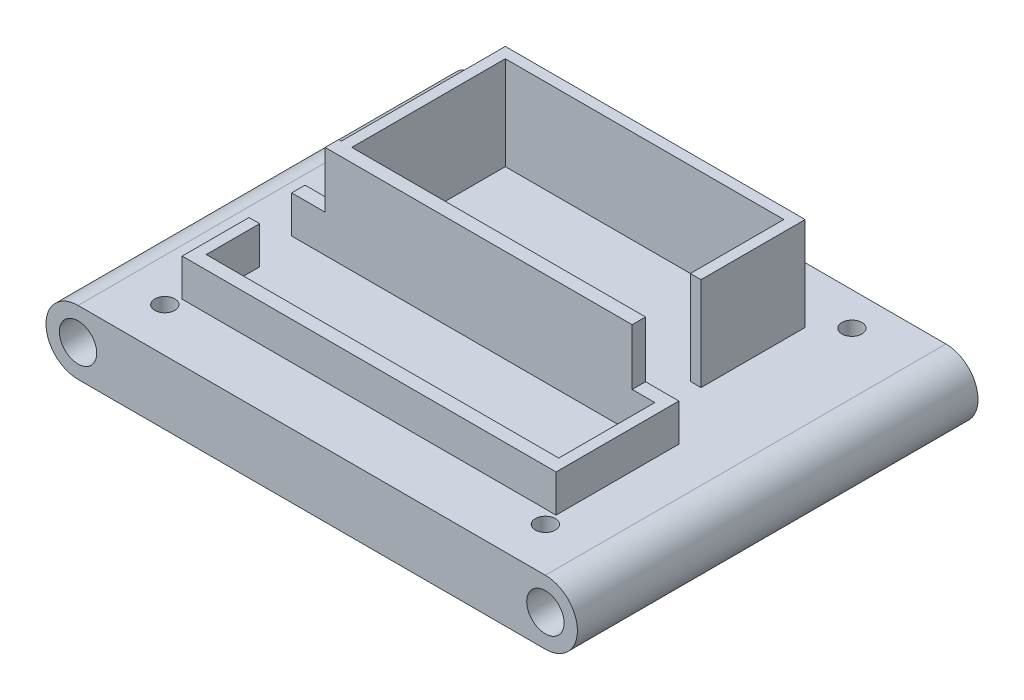
SolidWorks part; units mm, degrees
ref_plane "Front Plane" through (0, 0, 0) normal (0, 0, 1) x (1, 0, 0)
ref_plane "Top Plane" through (0, 0, 0) normal (0, 1, 0) x (1, 0, 0)
ref_plane "Right Plane" through (0, 0, 0) normal (1, 0, 0) x (0, 0, -1)
sketch "Sketch1" plane through (0, 0, 0) normal (0, 0, 1) x (1, 0, 0)
  line L0 (0, -55) -> (0, 55) construction
  line L1 (-44.45, 6.096) -> (44.45, 6.096)
  line L2 (-44.45, -6.096) -> (44.45, -6.096)
  arc A0 (44.45, -6.096) -> (44.45, 6.096) centre (44.45, 0) ccw
  arc A1 (-44.45, -6.096) -> (-44.45, 6.096) centre (-44.45, 0) cw
  circle A2 centre (-44.45, 0) radius 3.556
  circle A3 centre (44.45, 0) radius 3.556
extrude "Boss-Extrude1" add sketch "Sketch1" along normal blind 76.2
sketch "Sketch2" plane through (0, -6.096, 0) normal (0, -1, 0) x (1, 0, 0)
  circle A0 centre (-9.144, 69.215) radius 1.905
  circle A1 centre (27.051, 60.833) radius 1.905
  circle A2 centre (-28.956, 69.215) radius 1.905
  circle A3 centre (-28.956, 6.985) radius 1.905
  circle A4 centre (-9.144, 6.985) radius 1.905
  circle A5 centre (11.049, 60.833) radius 1.905
  circle A6 centre (11.049, 15.367) radius 1.905
  circle A7 centre (27.051, 15.367) radius 1.905
  dimension "D1" = 2
  dimension "D2" = 2
  dimension "D3" = 2
  dimension "D4" = 2
extrude "Cut-Extrude1" cut sketch "Sketch2" against normal blind 6.604
sketch "Sketch3" plane through (0, 6.096, 0) normal (0, 1, 0) x (1, 0, 0)
  line L1 (-29.21, -12.7) -> (28.8477, -12.7)
  line L2 (-29.21, -12.7) -> (-29.21, -10.16)
  line L3 (-29.21, -10.16) -> (28.8477, -10.16)
  line L4 (28.8477, -12.7) -> (28.8477, -10.16)
  line L5 (-29.21, -44.45) -> (29.21, -44.45)
  line L6 (-29.21, -44.45) -> (-29.21, -41.91)
  line L7 (-29.21, -41.91) -> (29.21, -41.91)
  line L8 (29.21, -44.45) -> (29.21, -41.91)
  line L9 (-29.21, -41.91) -> (-26.67, -41.91)
  line L10 (-29.21, -41.91) -> (-29.21, -15.24)
  line L11 (-29.21, -15.24) -> (-26.67, -15.24)
  line L12 (-26.67, -41.91) -> (-26.67, -15.24)
  line L17 (28.8477, -15.24) -> (26.3077, -15.24)
  line L18 (28.8477, -15.24) -> (28.8477, -30.48)
  line L19 (28.8477, -30.48) -> (26.3077, -30.48)
  line L20 (26.3077, -15.24) -> (26.3077, -30.48)
  line L21 (-29.21, -12.7) -> (-26.67, -12.7)
  line L22 (-29.21, -12.7) -> (-29.21, -15.24)
  line L23 (-29.21, -15.24) -> (-26.67, -15.24)
  line L24 (-26.67, -12.7) -> (-26.67, -15.24)
  line L25 (28.8477, -12.7) -> (26.3077, -12.7)
  line L26 (28.8477, -12.7) -> (28.8477, -15.24)
  line L27 (28.8477, -15.24) -> (26.3077, -15.24)
  line L28 (26.3077, -12.7) -> (26.3077, -15.24)
  point P0 (0, 0)
  point P1 (0, 0)
  dimension "D1" = 2.54
  dimension "D2" = 2.54
  dimension "D3" = 58.42
  dimension "D4" = 2.54
  dimension "D5" = 2.54
  dimension "D6" = 15.24
extrude "Boss-Extrude2" add sketch "Sketch3" along normal blind 17.78 contours L1 L4 L3 L2 | L7 L12 L1 L10 | L5 L8 L7 L6 | L24 L1 L22 L11 | L1 L28 L17 L26
sketch "Sketch4" plane through (0, 6.096, 0) normal (0, 1, 0) x (1, 0, 0)
  line L1 (29.21, -44.45) -> (36.068, -44.45)
  line L2 (29.21, -44.45) -> (29.21, -41.91)
  line L3 (29.21, -41.91) -> (36.068, -41.91)
  line L4 (36.068, -44.45) -> (36.068, -41.91)
  line L5 (-29.21, -44.45) -> (-36.068, -44.45)
  line L6 (-29.21, -44.45) -> (-29.21, -41.91)
  line L7 (-29.21, -41.91) -> (-36.068, -41.91)
  line L8 (-36.068, -44.45) -> (-36.068, -41.91)
  line L13 (36.068, -44.45) -> (33.528, -44.45)
  line L14 (36.068, -44.45) -> (36.068, -62.738)
  line L15 (36.068, -62.738) -> (33.528, -62.738)
  line L16 (33.528, -44.45) -> (33.528, -62.738)
  line L17 (-36.068, -62.738) -> (36.068, -62.738)
  line L18 (-36.068, -62.738) -> (-36.068, -65.278)
  line L19 (-36.068, -65.278) -> (36.068, -65.278)
  line L20 (36.068, -62.738) -> (36.068, -65.278)
  line L21 (-36.068, -62.738) -> (-33.528, -62.738)
  line L22 (-36.068, -62.738) -> (-36.068, -52.578)
  line L23 (-36.068, -52.578) -> (-33.528, -52.578)
  line L24 (-33.528, -62.738) -> (-33.528, -52.578)
  line M19 (-29.21, -44.45) -> (-29.21, -10.16)
  line M27 (29.21, -41.91) -> (29.21, -44.45)
  dimension "D1" = 6.858
  dimension "D2" = 6.858
  dimension "D3" = 10.16
  dimension "D5" = 18.288
  dimension "D6" = 2.54
  dimension "D7" = 2.54
extrude "Boss-Extrude3" add sketch "Sketch4" along normal blind 7.112 contours L8 L5 L7 M19 | L17 L24 L23 L22 | L20 L15 L17 L18 L19 | L1 L16 L15 L14 | L1 L4 L3 M27
sketch "Sketch5" plane through (0, 6.096, 0) normal (0, 1, 0) x (1, 0, 0)
  circle A2 centre (36.068, -67.818) radius 1.905
  circle A3 centre (32.9117, -6.35) radius 1.905
extrude "Cut-Extrude3" cut sketch "Sketch5" against normal blind 7.112 contours A2 | A3
sketch "Sketch6" plane through (0, 6.096, 0) normal (0, 1, 0) x (1, 0, 0)
  circle A0 centre (-36.322, -67.818) radius 1.905
  circle A1 centre (-33.274, -6.35) radius 1.905
extrude "Cut-Extrude4" cut sketch "Sketch6" against normal blind 7.112 contours A1 | A0
sketch "Sketch8" plane through (0, 23.876, 0) normal (0, 1, 0) x (1, 0, 0)
  line L2 (28.3397, -30.48) -> (28.3397, -10.16)
  line L3 (28.3397, -30.48) -> (28.3397, -10.16)
  line L4 (28.3397, -10.16) -> (28.8477, -10.16)
  line L5 (-28.702, -41.91) -> (-28.702, -10.16)
  line L6 (-28.702, -41.91) -> (-28.702, -10.16)
  line L7 (28.8477, -10.16) -> (28.8477, -30.48)
  line L8 (28.8477, -30.48) -> (28.3397, -30.48)
  line L9 (-28.702, -10.16) -> (-29.21, -10.16)
  line L10 (-29.21, -10.16) -> (-29.21, -41.8259)
  line L11 (-29.21, -44.45) -> (-29.21, -10.16) construction
  line L12 (-29.21, -41.8259) -> (-28.702, -41.91)
  dimension "D1" = 0.508
  dimension "D2" = 0.508
extrude "Cut-Extrude5" cut sketch "Sketch8" against normal up to surface (17.78 mm away) up to face at (-33.274, 6.096, 8.255)
sketch "Sketch9" plane through (0, 13.208, 0) normal (0, 1, 0) x (1, 0, 0)
  line L1 (-35.56, -41.91) -> (-36.068, -41.91)
  line L2 (-35.56, -44.45) -> (-35.56, -41.91)
  line L3 (-35.56, -44.45) -> (-35.56, -41.91)
  line L4 (-36.068, -41.91) -> (-36.068, -44.45)
  line L5 (-36.068, -44.45) -> (-35.56, -44.45)
  dimension "D1" = 0.508
extrude "Cut-Extrude6" cut sketch "Sketch9" against normal up to surface (7.112 mm away) up to face at (-6.6003, 6.096, 40.4072)
sketch "Sketch10" plane through (0, 13.208, 0) normal (0, 1, 0) x (1, 0, 0)
  line L8 (-35.56, -65.278) -> (-35.56, -52.578)
  line L9 (-35.56, -65.278) -> (-35.56, -52.578)
  line L10 (-35.56, -52.578) -> (-36.068, -52.578)
  line L11 (35.56, -41.91) -> (35.56, -65.278)
  line L12 (35.56, -41.91) -> (35.56, -65.278)
  line L13 (-36.068, -52.578) -> (-36.068, -65.278)
  line L14 (-36.068, -65.278) -> (-35.56, -65.278)
  line L15 (35.56, -41.91) -> (36.068, -41.91)
  line L16 (36.068, -41.91) -> (36.068, -65.278)
  line L17 (36.068, -65.278) -> (35.56, -65.278)
  line M3 (-36.068, -52.578) -> (-36.068, -65.278)
  line M4 (-36.068, -65.278) -> (36.068, -65.278)
  line M5 (36.068, -65.278) -> (36.068, -41.91)
  line M6 (36.068, -41.91) -> (29.21, -41.91)
  line M12 (-33.528, -52.578) -> (-36.068, -52.578)
  dimension "D1" = 0.508
  dimension "D2" = 0.508
extrude "Cut-Extrude7" cut sketch "Sketch10" against normal up to surface (7.112 mm away) contours L9 M4 M12 M3 | L12 M6 M4 M5 up to face at (-6.5495, 6.096, 40.4072)
sketch "Sketch11" plane through (0, 23.876, 0) normal (0, 1, 0) x (1, 0, 0)
  line L1 (-28.702, -10.668) -> (-28.702, -10.16)
  line L2 (-28.702, -10.668) -> (28.3397, -10.668)
  line L3 (-28.702, -10.668) -> (28.3397, -10.668)
  line L4 (-28.702, -10.16) -> (28.3397, -10.16)
  line L5 (28.3397, -10.16) -> (28.3397, -10.668)
  line M5 (28.3397, -30.48) -> (28.3397, -10.16)
  line M6 (28.3397, -10.16) -> (-28.702, -10.16)
  line M7 (-28.702, -10.16) -> (-28.702, -41.91)
  dimension "D1" = 0.508
extrude "Cut-Extrude8" cut sketch "Sketch11" against normal up to surface (17.78 mm away) contours L3 M7 M5 M6 up to face at (-6.5495, 6.096, 40.4072)
